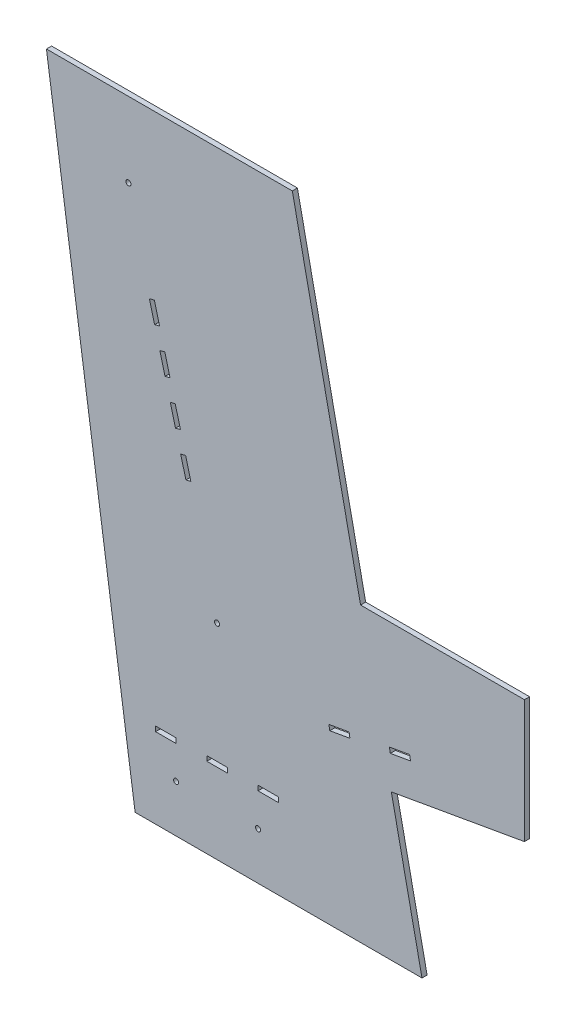
SolidWorks part; units mm, degrees
ref_plane "Front Plane" through (0, 0, 0) normal (0, 0, 1) x (1, 0, 0)
ref_plane "Top Plane" through (0, 0, 0) normal (0, 1, 0) x (1, 0, 0)
ref_plane "Right Plane" through (0, 0, 0) normal (1, 0, 0) x (0, 0, -1)
sketch "Sketch1" plane through (0, 0, 0) normal (0, 0, 1) x (1, 0, 0)
  line L0 (0, 0) -> (-177.8, 0)
  line L1 (-177.8, 0) -> (-232.7656, 382.27)
  line L2 (-232.7656, 382.27) -> (-80.3656, 382.27)
  line L3 (-80.3656, 382.27) -> (0, 0)
  dimension "D1" = 382.27
  dimension "D2" = 177.8
  dimension "D3" = 152.4
  dimension "D4" = 54.9656
extrude "Boss-Extrude1" add sketch "Sketch1" along normal blind 3.175
sketch "Sketch2" plane through (0, 0, 3.175) normal (0, 0, 1) x (1, 0, 0)
  line L0 (-177.8, 0) -> (0, 0) construction
  circle A0 centre (-127, 127) radius 1.5875
  circle A1 centre (-181.958, 335.788) radius 1.5875
  dimension "D1" = 3.175
  dimension "D2" = 3.175
  dimension "D3" = 208.788
  dimension "D4" = 54.958
  dimension "D5" = 127
  dimension "D6" = 127
extrude "Cut-Extrude1" cut sketch "Sketch2" against normal blind 3.175
sketch "Sketch3" plane through (0, 0, 3.175) normal (0, 0, 1) x (1, 0, 0)
  line L1 (-63.5, 82.55) -> (63.5, 104.9435)
  line L2 (-63.5, 82.55) -> (-63.5, 181.1435)
  line L3 (-63.5, 181.1435) -> (63.5, 181.1435)
  line L4 (63.5, 104.9435) -> (63.5, 181.1435)
  line L5 (-177.8, 0) -> (0, 0) construction
  circle A0 centre (-127, 127) radius 1.5875 construction
  dimension "D1" = 127
  dimension "D2" = 76.2
  dimension "D3" = 44.45
  dimension "D4" = 63.5
  dimension "D5" = 10
extrude "Boss-Extrude2" add sketch "Sketch3" against normal blind 3.175
sketch "Sketch4" plane through (0, 0, 3.175) normal (0, 0, 1) x (1, 0, 0)
  line L0 (-57.15, 104.14) -> (-44.6429, 106.3453)
  line L1 (-45.1943, 109.4721) -> (-57.7013, 107.2668)
  line L2 (-57.7013, 107.2668) -> (-57.15, 104.14)
  line L3 (-45.1943, 109.4721) -> (-44.6429, 106.3453)
  line L4 (-19.6288, 110.756) -> (-7.1218, 112.9613)
  line L5 (-7.6731, 116.0881) -> (-20.1802, 113.8828)
  line L6 (-20.1802, 113.8828) -> (-19.6288, 110.756)
  line L7 (-7.6731, 116.0881) -> (-7.1218, 112.9613)
  line L8 (-19.0041, 90.3958) -> (63.5, 104.9435) construction
  circle A0 centre (-127, 127) radius 1.5875 construction
  dimension "D1" = 3.175
  dimension "D2" = 12.7
  dimension "D3" = 3.175
  dimension "D4" = 12.7
  dimension "D5" = 0
  dimension "D6" = 25.4
  dimension "D7" = 69.85
  dimension "D8" = 22.86
  dimension "D9" = 0
extrude "Cut-Extrude2" cut sketch "Sketch4" against normal blind 3.175
sketch "Sketch5" plane through (0, 0, 3.175) normal (0, 0, 1) x (1, 0, 0)
  line L0 (-127, 127) -> (-181.958, 335.788)
  line L1 (-146.3157, 194.145) -> (-143.2453, 194.9532)
  line L2 (-143.2453, 194.9532) -> (-146.4781, 207.2348)
  line L3 (-146.4781, 207.2348) -> (-149.5486, 206.4266)
  line L4 (-149.5486, 206.4266) -> (-146.3157, 194.145)
  dimension "D1" = 90
  dimension "D2" = 3.175
  dimension "D3" = 1.5875
  dimension "D4" = 69.85
  dimension "D5" = 12.7
extrude "Cut-Extrude3" cut sketch "Sketch5" against normal blind 10.16 contours L2 L3 L0 L1 | L3 L4 L1 L0
pattern_linear "LPattern1" count 4 spacing 25.4 along (-0.2546, 0.9671, 0) of "Cut-Extrude3"
sketch "Sketch6" plane through (0, 0, 3.175) normal (0, 0, 1) x (1, 0, 0)
  line L1 (-165.1, 52.705) -> (-152.4, 52.705)
  line L2 (-165.1, 52.705) -> (-165.1, 49.657)
  line L3 (-165.1, 49.657) -> (-152.4, 49.657)
  line L4 (-152.4, 52.705) -> (-152.4, 49.657)
  circle A0 centre (-127, 127) radius 1.5875 construction
  dimension "D1" = 74.295
  dimension "D2" = 12.7
  dimension "D3" = 3.048
  dimension "D4" = 38.1
extrude "Cut-Extrude4" cut sketch "Sketch6" against normal blind 5.08
pattern_linear "LPattern2" count 3 spacing 31.75 along (1, 0, 0) of "Cut-Extrude4"
sketch "Sketch7" plane through (0, 0, 3.175) normal (0, 0, 1) x (1, 0, 0)
  line L0 (-101.6, 49.657) -> (-88.9, 49.657) construction
  line L1 (-165.1, 49.657) -> (-152.4, 49.657) construction
  line L2 (-165.1, 52.705) -> (-165.1, 49.657) construction
  line L3 (-88.9, 49.657) -> (-88.9, 52.705) construction
  circle A0 centre (-152.4, 29.337) radius 1.5875
  circle A1 centre (-101.6, 29.337) radius 1.5875
  dimension "D1" = 3.175
  dimension "D2" = 3.175
  dimension "D3" = 20.32
  dimension "D4" = 20.32
  dimension "D5" = 12.7
  dimension "D6" = 12.7
extrude "Cut-Extrude5" cut sketch "Sketch7" against normal blind 19.05
